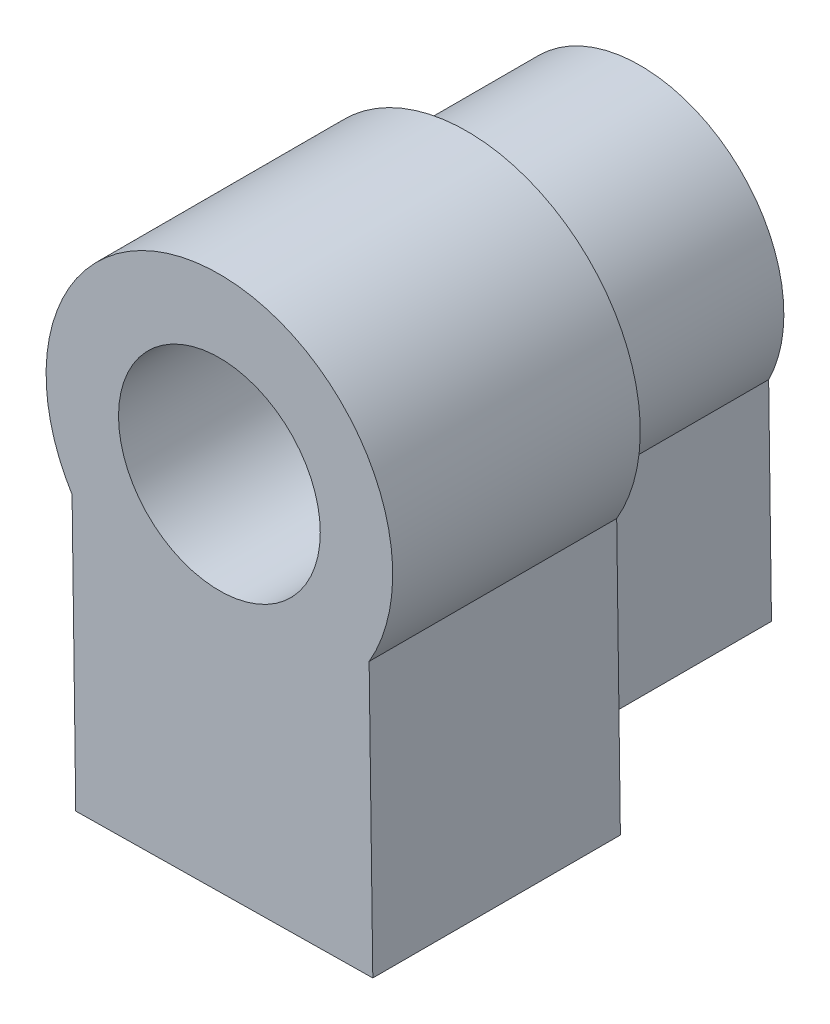
SolidWorks part; units mm, degrees
ref_plane "Front Plane" through (0, 0, 0) normal (0, 0, 1) x (1, 0, 0)
ref_plane "Top Plane" through (0, 0, 0) normal (0, 1, 0) x (1, 0, 0)
ref_plane "Right Plane" through (0, 0, 0) normal (1, 0, 0) x (0, 0, -1)
sketch "Sketch1" plane through (0, 0, 0) normal (0, 0, 1) x (1, 0, 0)
  line L0 (-5.2495, -4.7726) -> (5.0505, -4.6333)
  line L1 (-5.2495, -4.7726) -> (-5.1359, -13.1726)
  line L2 (5.0505, -4.6333) -> (5.1641, -13.0333)
  line L3 (-5.1359, -13.1726) -> (5.1641, -13.0333)
  circle A0 centre (-0.1356, -2.0362) radius 5.8
  dimension "D1" = 11.6
  dimension "D2" = 5.8
  dimension "D3" = 5.8
  dimension "D4" = 10.3
  dimension "D5" = 8.4
extrude "Boss-Extrude1" add sketch "Sketch1" along normal blind 7 contours A0 L1 L3 L2 | L0 A0 | L0 A0
sketch "Sketch2" plane through (0, 0, 7) normal (0, 0, 1) x (1, 0, 0)
  line L0 (5.9126, -5.5603) -> (-6.0863, -5.7226)
  line L1 (5.9126, -5.5603) -> (6.0614, -16.5603)
  line L2 (-6.0863, -5.7226) -> (-5.9375, -16.7226)
  line L3 (6.0614, -16.5603) -> (-5.9375, -16.7226)
  line L4 (-5.1359, -13.1726) -> (5.1641, -13.0333) construction
  circle A0 centre (-0.1356, -2.0362) radius 7
  arc A1 (5.0505, -4.6333) -> (-5.2495, -4.7726) centre (-0.1356, -2.0362) ccw construction
  circle A2 centre (-0.1356, -2.0362) radius 4.075
  line M1 (5.1641, -13.0333) -> (5.0505, -4.6333)
  arc M2 (5.0505, -4.6333) -> (-5.2495, -4.7726) centre (-0.1356, -2.0362) ccw
  line M3 (-5.2495, -4.7726) -> (-5.1359, -13.1726)
  line M4 (-5.1359, -13.1726) -> (5.1641, -13.0333)
  dimension "D1" = 0
  dimension "D2" = 14
  dimension "D3" = 0
  dimension "D4" = 8.15
  dimension "D5" = 7
  dimension "D6" = 7
  dimension "D7" = 12
  dimension "D8" = 180
  dimension "D9" = 11
extrude "Boss-Extrude3" add sketch "Sketch2" along normal blind 10 contours L0 A0 M3 M2 M1 | A2 L0 M1 M2 M3 | A2 L0 A0 M3 M1 | A0 M3 M4 M1 | A0 L2 L3 L1 M1 M4 M3 | A0 L0 M1 | L0 A0 M3
sketch "Sketch6" plane through (0.225, -16.6392, 0) normal (0.0135, -0.9999, 0) x (-0.9999, -0.0135, 0)
  line L0 (-5.8369, -17) -> (6.1631, -17) construction
  circle A0 centre (0.2412, -13) radius 1.35
  point P2 (0.1631, -17)
  dimension "D2" = 2.7
  dimension "D1" = 4
extrude "Cut-Extrude3" cut sketch "Sketch6" against normal blind 8.5
